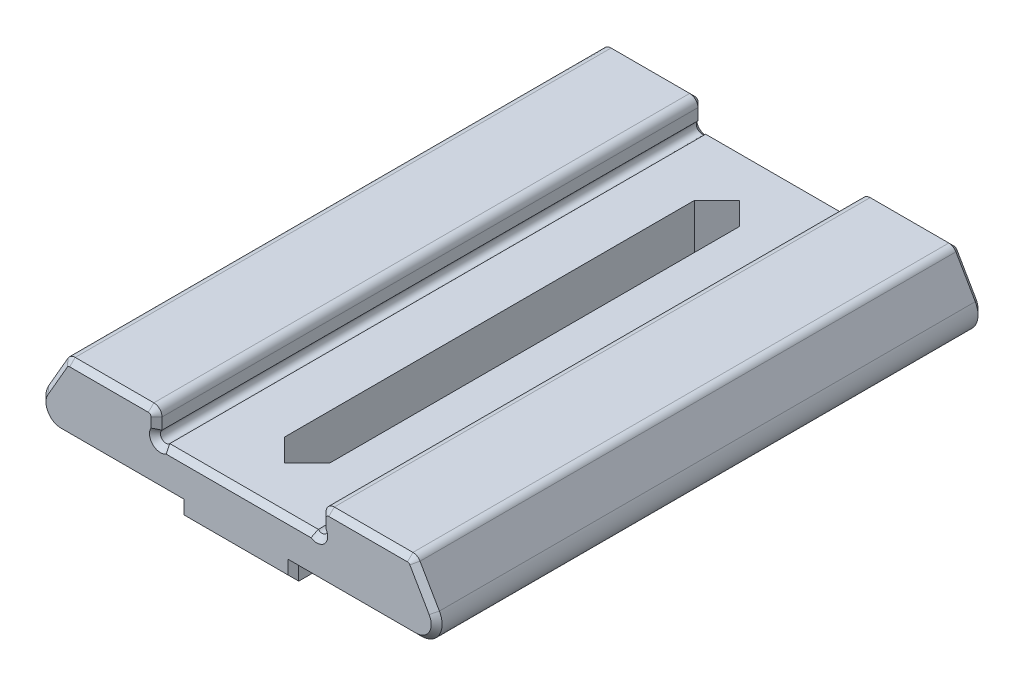
SolidWorks part; units mm, degrees
ref_plane "Front Plane" through (0, 0, 0) normal (0, 0, 1) x (1, 0, 0)
ref_plane "Top Plane" through (0, 0, 0) normal (0, 1, 0) x (1, 0, 0)
ref_plane "Right Plane" through (0, 0, 0) normal (1, 0, 0) x (0, 0, -1)
sketch "Sketch1" plane through (0, 0, 0) normal (0, 0, 1) x (1, 0, 0)
  line L0 (-12.9887, 0) -> (0, 0)
  line L2 (0, 0) -> (12.9887, 0)
  line L3 (14.2877, 2.25) -> (12.7, 5)
  line L4 (12.7, 5) -> (6, 5)
  line L5 (6, 5) -> (6, 3.5657)
  line L6 (6, 3) -> (5.4343, 3) construction
  line L7 (-6, 3) -> (-6, 3.5657) construction
  line L8 (-6, 5) -> (-12.7, 5)
  line L9 (-12.7, 5) -> (-14.2877, 2.25)
  line L10 (-6, 3) -> (-5.4343, 3.5657) construction
  line L11 (6, 3) -> (5.4343, 3.5657) construction
  line L12 (-5.4343, 3) -> (-6, 3) construction
  line L13 (-6, 3.5657) -> (-6, 5)
  line L14 (6, 3.5657) -> (6, 3) construction
  line L15 (5.4343, 3) -> (-5.4343, 3)
  arc A0 (14.2877, 2.25) -> (12.9887, 0) centre (12.9887, 1.5) cw
  arc A1 (-12.9887, 0) -> (-14.2877, 2.25) centre (-12.9887, 1.5) cw
  arc A2 (-6, 3.5657) -> (-5.4343, 3) centre (-5.7172, 3.2828) ccw
  arc A3 (6, 3.5657) -> (5.4343, 3) centre (5.7172, 3.2828) ccw construction
  arc A4 (-5.4343, 3) -> (-6, 3.5657) centre (-5.7172, 3.2828) ccw construction
  arc A5 (5.4343, 3) -> (6, 3.5657) centre (5.7172, 3.2828) ccw
  point P15 (5.648, 1.9737)
  point P21 (0, 0)
  point P22 (-5.982, 2.4409)
  point P23 (-5.9504, 2.3238)
  point P24 (-5.5757, 2)
  point P27 (-6, 2.4243)
  point P28 (-6.028, 2.392)
  point P29 (-5.589, 1.9875)
  point P31 (0, 0)
  point P32 (5.5757, 2)
  point P33 (6, 2.4243)
  point P34 (5.5583, 2.019)
  point P35 (5.9789, 2.4435)
  point P36 (0, 0)
  point P37 (0, 0)
  point P38 (0, 0)
  dimension "D6" = 6.7
  dimension "D7" = 0.8
  dimension "D8" = 0.8
  dimension "D2" = 120
  dimension "D3" = 6
  dimension "D4" = 2
  dimension "D5" = 12
  dimension "D9" = 45
  dimension "D10" = 45
  dimension "D11" = 5
extrude "Boss-Extrude1" add sketch "Sketch1" against normal blind 40
sketch "Sketch2" plane through (0, 0, 0) normal (0, -1, 0) x (1, 0, 0)
  line L0 (4, 0) -> (4, -40)
  line L1 (4, -40) -> (-4, -40)
  line L2 (-4, -40) -> (-4, 0)
  line L3 (-4, 0) -> (4, 0)
  line L5 (-12.9887, 0) -> (12.9887, 0) construction
  dimension "D1" = 8
  dimension "D3" = 40
extrude "Boss-Extrude2" add sketch "Sketch2" along normal blind 1
sketch "Sketch3" plane through (0, 3, 0) normal (0, 1, 0) x (1, 0, 0)
  line L0 (0, 3.35) -> (1.65, 5)
  line L1 (1.65, 5) -> (1.65, 35)
  line L2 (1.65, 35) -> (0, 36.65)
  line L3 (0, 36.65) -> (-1.65, 35)
  line L4 (-1.65, 35) -> (-1.65, 5)
  line L5 (-1.65, 5) -> (0, 3.35)
  line L6 (5.4343, 40) -> (-5.4343, 40) construction
  line L8 (0, 0) -> (0, 40) construction
  line L10 (-1.65, 20) -> (1.65, 20) construction
  point P6 (0, -40)
  point P10 (0, 20)
  dimension "D1" = 3.3
  dimension "D2" = 33.3
extrude "Cut-Extrude1" cut sketch "Sketch3" against normal through all
fillet "Fillet1" radius 0.6 4 edges at (6, 5, -20) (12.7, 5, -20) (-12.7, 5, -20) (-6, 5, -20)
chamfer "Chamfer1" distance 0.4 angle 45 39 edges at (9.4768, 5, -40) (6.1757, 4.8243, -40) (12.6536, 4.9196, -40) (6, 3.9828, -40) (13.5805, 3.475, -40) (0, 3, -40) (14.2877, 0.75, -40) (-6, 3.9828, -40) (8.4943, 0, -40) (-6.1757, 4.8243, -40) (4, -0.5, -40) (-9.4768, 5, -40) (0, -1, -40) (-12.6536, 4.9196, -40) (-4, -0.5, -40) (-13.5805, 3.475, -40) (-8.4943, 0, -40) (-14.2877, 0.75, -40) (0, -1, 0) (4, -0.5, 0) (8.4943, 0, 0) (14.2877, 0.75, 0) (13.5805, 3.475, 0) (-8.4943, 0, 0) (12.6536, 4.9196, 0) (-14.2877, 0.75, 0) (9.4768, 5, 0) (-13.5805, 3.475, 0) (6.1757, 4.8243, 0) (-12.6536, 4.9196, 0) (6, 3.9828, 0) (-9.4768, 5, 0) (0, 3, 0) (-6.1757, 4.8243, 0) (-6, 3.9828, 0) (6, 3, -40) (-6, 3, -40) (6, 3, 0) (-6, 3, 0)
